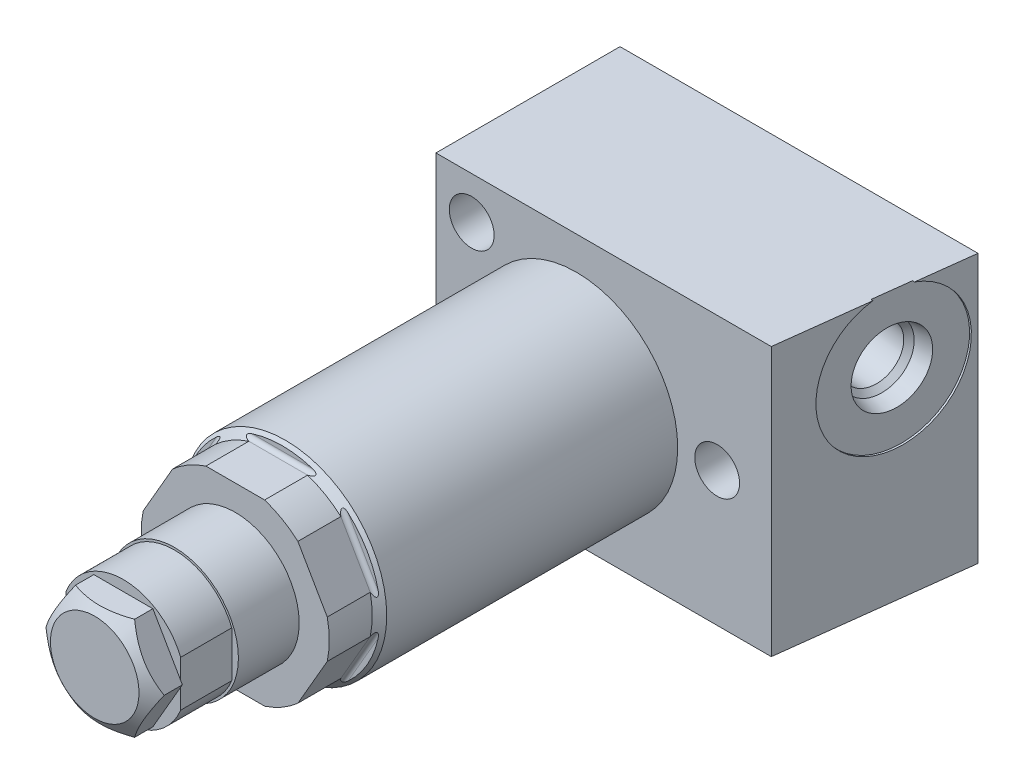
SolidWorks part; units mm, degrees
material "Alloy Steel"
ref_plane "Front Plane" through (0, 0, 0) normal (0, 0, 1) x (1, 0, 0)
ref_plane "Top Plane" through (0, 0, 0) normal (0, 1, 0) x (1, 0, 0)
ref_plane "Right Plane" through (0, 0, 0) normal (1, 0, 0) x (0, 0, -1)
ref_plane "Plane1" through (0, 0, 0) normal (0, 0, 1) x (1, 0, 0)
sketch "Sketch1" plane through (0, 0, 0) normal (0, 0, 1) x (1, 0, 0)
  circle A0 centre (0, 0) radius 12.573
  dimension "D1" = 25.146
extrude "Extrude1" add sketch "Sketch1" along normal blind 55.8292
ref_plane "Plane2" through (0, 0, 0) normal (1, 0, 0) x (0, 0, 1)
sketch "Sketch2" plane through (0, 0, 0) normal (1, 0, 0) x (0, 0, 1)
  line L0 (49.9872, 12.573) -> (49.9872, 11.5951)
  line L1 (50.4952, 11.0871) -> (55.8292, 11.0871)
  line L2 (36.4871, 0) -> (42.9133, 0) construction
  line L3 (49.9872, 12.573) -> (55.8292, 12.573)
  line L4 (55.8292, 12.573) -> (0, 12.573) construction
  line L5 (55.8292, 12.573) -> (55.8292, 11.0871)
  line L6 (55.8292, -12.573) -> (55.8292, 12.573) construction
  arc A0 (49.9872, 11.5951) -> (50.4952, 11.0871) centre (50.4952, 11.5951) ccw
  dimension "D2" = 0.508
  dimension "D1" = 22.1742
  dimension "D3" = 5.842
extrude "Cut-Extrude1" cut sketch "Sketch2" against normal mid plane 30.1752
ref_plane "Plane12" through (0, 0, 0) normal (1, 0, 0) x (0, 0, -1)
sketch "Sketch10" plane through (0, 0, 0) normal (1, 0, 0) x (0, 0, -1)
  line L0 (-55.8292, 11.6713) -> (-50.4952, 11.6713)
  line L1 (-50.4952, 11.6713) -> (-49.5935, 12.573)
  line L2 (-49.5935, 12.573) -> (-55.8292, 12.573)
  line L3 (-55.8292, 12.573) -> (-55.8292, 11.6713)
  line L4 (-42.933, 0) -> (-36.0737, 0) construction
  line L5 (-55.8292, 12.573) -> (-55.8292, -11.0871) construction
  line L6 (0, 12.573) -> (-55.8292, 12.573) construction
  dimension "D1" = 5.334
  dimension "D2" = 23.3426
  dimension "D3" = 45
revolve "Cut-Revolve1" cut sketch "Sketch10" angle 360 about L4
ref_plane "Plane14" through (0, 0, 0) normal (1, 0, 0) x (0, 0, -1)
sketch "Sketch12" plane through (0, 0, 0) normal (1, 0, 0) x (0, 0, -1)
  line L0 (-55.8292, 0) -> (-69.723, 0)
  line L1 (-69.723, 0) -> (-69.723, 7.9375)
  line L2 (-69.723, 7.9375) -> (-55.8292, 7.9375)
  line L3 (-55.8292, 7.9375) -> (-55.8292, 0)
  line L4 (-54.276, 0) -> (-25.1182, 0) construction
  line L5 (-55.8292, 11.6713) -> (-55.8292, -11.0871) construction
  dimension "D1" = 13.8938
  dimension "D2" = 15.875
revolve "Revolve1" add sketch "Sketch12" angle 360 about L4
ref_plane "Plane16" through (0, 0, 47.371) normal (0, 0, -1) x (0, 1, 0)
sketch "Sketch15" plane through (0, 0, 69.723) normal (0, 0, -1) x (0, 1, 0)
  line L0 (-3.5247, 7.112) -> (3.5247, 7.112)
  line L1 (-3.5247, -7.112) -> (3.5247, -7.112)
  line L2 (-8.7312, 0) -> (8.7312, 0) construction
  arc A0 (3.5247, 7.112) -> (-3.5247, 7.112) centre (0, 0) ccw
  arc A2 (-3.5247, -7.112) -> (3.5247, -7.112) centre (0, 0) ccw
  dimension "D2" = 7.9375
  dimension "D1" = 14.224
extrude "Cut-Extrude10" cut sketch "Sketch15" along normal blind 6.35
sketch "Sketch16" plane through (0, 0, 69.723) normal (0, 0, 1) x (1, 0, 0)
  line L0 (-3.6662, 6.35) -> (3.6662, 6.35)
  line L1 (3.6662, 6.35) -> (7.3323, 0)
  line L2 (7.3323, 0) -> (3.6662, -6.35)
  line L3 (3.6662, -6.35) -> (-3.6662, -6.35)
  line L4 (-3.6662, -6.35) -> (-7.3323, 0)
  line L5 (-7.3323, 0) -> (-3.6662, 6.35)
  line L6 (-8.0656, 0) -> (8.0656, 0) construction
  dimension "D1" = 12.7
extrude "Extrude2" add sketch "Sketch16" along normal blind 3.556
ref_plane "Plane18" through (0, 0, 0) normal (0, 1, 0) x (1, 0, 0)
sketch "Sketch17" plane through (0, 0, 0) normal (0, 1, 0) x (1, 0, 0)
  line L0 (5.4991, -73.279) -> (7.3323, -71.9953)
  line L1 (0, -57.3412) -> (0, -51.7219) construction
  line L2 (5.4991, -73.279) -> (7.3323, -73.279)
  line L3 (7.3323, -73.279) -> (7.3323, -71.9953)
  dimension "D1" = 35
  dimension "D2" = 10.9982
revolve "Cut-Revolve4" cut sketch "Sketch17" angle 360 about L1
ref_plane "Plane19" through (0, 0, 0) normal (0, 1, 0) x (-1, 0, 0)
sketch "Sketch18" plane through (0, 0, 0) normal (0, 1, 0) x (-1, 0, 0)
  line L0 (-27.0002, -9.398) -> (17.4498, -9.398)
  line L1 (17.4498, -9.398) -> (17.4498, 13.462)
  line L2 (17.4498, 13.462) -> (-24.1933, 13.462)
  line L3 (-24.1933, 13.462) -> (-27.0002, -9.398)
  line L4 (-12.573, 0) -> (12.573, 0) construction
  dimension "D1" = 9.398
  dimension "D2" = 22.86
  dimension "D3" = 17.4498
  dimension "D4" = 44.45
  dimension "D5" = 83
extrude "Extrude3" add sketch "Sketch18" along normal blind 16.6751 and the other way blind 16.6751
sketch "Sketch19" plane through (25.4624, 0, 3.1264) normal (0.9925, 0, 0.1219) x (0.1219, 0, -0.9925)
  circle A0 centre (3.2204, 8.3312) radius 8.6614
extrude "Cut-Extrude11" cut sketch "Sketch19" against normal blind 0.254
ref_plane "Plane20" through (25.6028, 8.3312, -0.101) normal (0, 1, 0) x (-0.1219, 0, 0.9925)
sketch "S2D0001" plane through (25.6028, 8.3312, -0.101) normal (0, 1, 0) x (-0.1219, 0, 0.9925)
  line L0 (0, 0) -> (4.5466, 0)
  line L1 (4.5466, 0) -> (4.1066, -2.0701)
  line L2 (4.1066, -2.0701) -> (3.4544, -2.7223)
  line L3 (3.4544, -2.7223) -> (3.4544, -12.192)
  line L4 (3.4544, -12.192) -> (0, -12.192)
  line L5 (0, -12.192) -> (0, 0)
  line L6 (0, -12.8016) -> (0, 0.6096) construction
  dimension "D1" = 12.192
revolve "Cut-Revolve5" cut sketch "S2D0001" angle 360 about L6
ref_plane "Plane21" through (17.4752, -9.7346, -8.3565) normal (0, 1, 0) x (-1, 0, 0)
sketch "Sketch21" plane through (17.4752, -9.7346, -8.3565) normal (0, 1, 0) x (-1, 0, 0)
  line L0 (0, -1.0415) -> (6.35, -1.0415)
  line L1 (6.35, -1.0415) -> (6.35, 1.4985)
  line L2 (6.35, 1.4985) -> (3.4544, 1.4985)
  line L3 (3.4544, 1.4985) -> (3.4544, 13.6905)
  line L4 (3.4544, 13.6905) -> (0, 15.7661)
  line L5 (0, 15.7661) -> (0, -1.0415)
  line L6 (0, -1.8819) -> (0, 16.6065) construction
revolve "Cut-Revolve6" cut sketch "Sketch21" angle 360 about L6
ref_plane "Plane22" through (17.4752, -9.7346, -8.3565) normal (0, 1, 0) x (-1, 0, 0)
sketch "Sketch22" plane through (17.4752, -9.7346, -8.3565) normal (0, 1, 0) x (-1, 0, 0)
  line L0 (0, -1.1685) -> (0, 1.6255) construction
  circle A0 centre (-5.08, 0.2285) radius 1.27
revolve "Revolve2" add sketch "Sketch22" angle 360 about L0
pattern_circular "CirPattern2" count 6 over 360 about axis through (0, 0, 0) along (0, 0, 1) of "Cut-Extrude1"
hole_wizard "Hole1" positions "Sketch24" profile "Sketch23" legacy end condition up to next
sketch "Sketch24" plane through (0, 0, 13.462) normal (0, 0, 1) x (1, 0, 0)
  line L0 (0, 0) -> (-19.4466, 0) construction
  point P0 (-13.0048, -11.43)
  point P1 (17.4752, 0)
  point P9 (-13.0048, 11.43)
  dimension "D1" = 17.4752
  dimension "D2" = 22.86
  dimension "D3" = 13.0048
sketch "Sketch23" plane through (-13.0048, -11.43, 13.462) normal (1, 0, 0) x (0, -1, 0)
  line L0 (0, 0) -> (0, 22.86)
  line L1 (0, 22.86) -> (2.7813, 22.86)
  line L2 (2.7813, 22.86) -> (2.7813, 0)
  line L3 (2.7813, 0) -> (0, 0)
  line L4 (0, 110) -> (0, -10) construction
  dimension "Diameter" = 5.5626
  dimension "Depth" = 22.86
sketch "Sketch27" plane through (0, 0, 0) normal (1, 0, 0) x (0, 0, -1)
  line L0 (9.398, 0) -> (-73.279, 0) construction
  line L2 (9.398, -16.6751) -> (9.398, 16.6751) construction
  line L3 (-73.279, 5.4991) -> (-73.279, -5.4991) construction
  line L4 (-63.373, 7.9375) -> (-63.373, 7.6581)
  line L6 (-55.8292, 7.9375) -> (-69.723, 7.9375) construction
  line L7 (-63.373, 7.6581) -> (-69.723, 7.6581)
  line L8 (-69.723, 7.9375) -> (-69.723, 3.5247) construction
  line L9 (-63.373, 7.9375) -> (-69.723, 7.9375)
  line L10 (-69.723, 7.9375) -> (-69.723, 7.6581)
  dimension "D1" = 6.35
  dimension "D2" = 15.3162
revolve "Cut-Revolve7" cut sketch "Sketch27" angle 360 about L0
